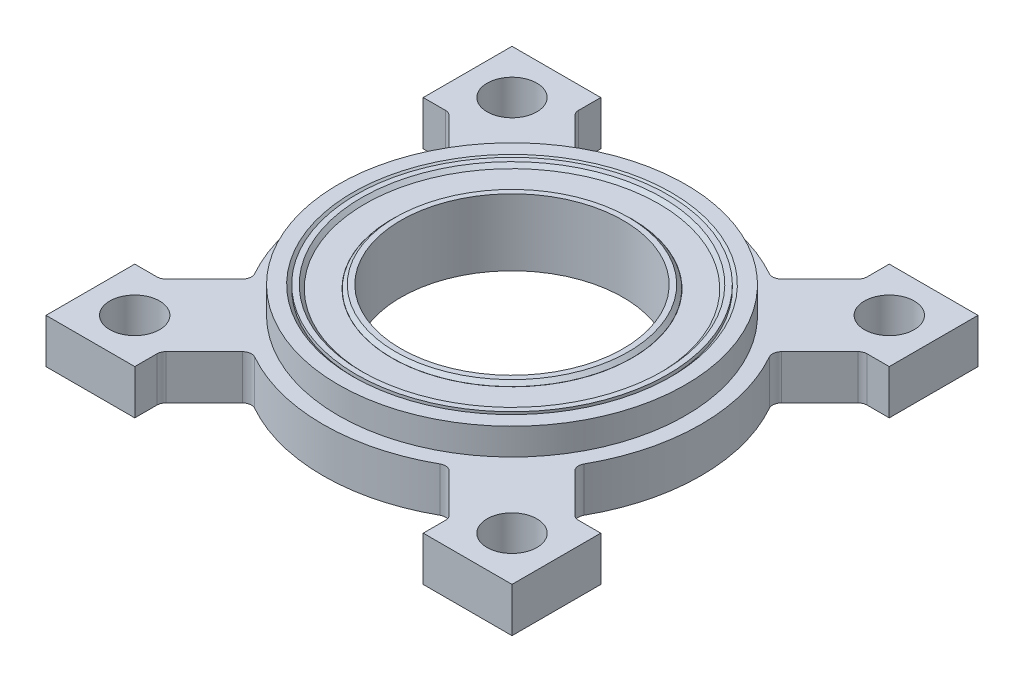
SolidWorks part; units mm, degrees
material "6061 Alloy"
ref_plane "Front Plane" through (0, 0, 0) normal (0, 0, 1) x (1, 0, 0)
ref_plane "Top Plane" through (0, 0, 0) normal (0, 1, 0) x (1, 0, 0)
ref_plane "Right Plane" through (0, 0, 0) normal (1, 0, 0) x (0, 0, -1)
sketch "Sketch1" plane through (0, 0, 0) normal (0, 1, 0) x (1, 0, 0)
  line L0 (-10.2997, 16.637) -> (-10.2997, 15.0529)
  line L1 (-16.637, -16.637) -> (-10.2997, -16.637)
  line L2 (-16.637, -16.637) -> (-16.637, -10.2997)
  line L3 (-16.637, 16.637) -> (-10.2997, 16.637)
  line L4 (16.637, -16.637) -> (16.637, -10.2997)
  line L5 (10.2997, 16.637) -> (16.637, 16.637)
  line L6 (-10.1137, 14.6038) -> (-7.0286, 11.5187)
  line L7 (-16.637, 10.2997) -> (-15.0529, 10.2997)
  line L8 (-16.637, -10.2997) -> (-15.0529, -10.2997)
  line L9 (10.2997, 16.637) -> (10.2997, 15.0529)
  line L10 (-10.2997, -15.0529) -> (-10.2997, -16.637)
  line L11 (-10.1137, -14.6038) -> (-7.3754, -11.8655)
  line L12 (15.0529, 10.2997) -> (16.637, 10.2997)
  line L13 (-14.6038, -10.1137) -> (-11.8655, -7.3754)
  line L14 (10.2997, -15.0529) -> (10.2997, -16.637)
  line L15 (-14.6038, 10.1137) -> (-11.8655, 7.3754)
  line L16 (15.0529, -10.2997) -> (16.637, -10.2997)
  line L17 (14.6038, 10.1137) -> (11.8655, 7.3754)
  line L18 (10.1137, 14.6038) -> (7.3754, 11.8655)
  line L19 (10.1137, -14.6038) -> (7.3754, -11.8655)
  line L20 (14.6038, -10.1137) -> (11.8655, -7.3754)
  line L21 (0, 0) -> (-16.637, -16.637) construction
  line L22 (-16.637, 10.2997) -> (-16.637, 16.637)
  line L23 (10.2997, -16.637) -> (16.637, -16.637)
  line L24 (16.637, 10.2997) -> (16.637, 16.637)
  circle A0 centre (0, 0) radius 11.1252
  circle A1 centre (-13.4704, -13.4704) radius 1.778
  circle A2 centre (-13.4704, 13.4704) radius 1.778
  circle A3 centre (13.4704, 13.4704) radius 1.778
  circle A4 centre (13.4704, -13.4704) radius 1.778
  arc A5 (11.761, -6.6151) -> (11.761, 6.6151) centre (0, 0) ccw
  arc A6 (-6.6151, -11.761) -> (6.6151, -11.761) centre (0, 0) ccw
  arc A7 (-11.761, 6.6151) -> (-11.761, -6.6151) centre (0, 0) ccw
  arc A8 (6.6151, 11.761) -> (-7.0286, 11.5187) centre (0, 0) ccw
  arc A9 (7.3754, 11.8655) -> (6.6151, 11.761) centre (6.9264, 12.3145) cw
  arc A10 (10.1137, 14.6038) -> (10.2997, 15.0529) centre (9.6647, 15.0529) ccw
  arc A11 (14.6038, 10.1137) -> (15.0529, 10.2997) centre (15.0529, 9.6647) cw
  arc A12 (11.8655, 7.3754) -> (11.761, 6.6151) centre (12.3145, 6.9264) ccw
  arc A13 (14.6038, -10.1137) -> (15.0529, -10.2997) centre (15.0529, -9.6647) ccw
  arc A14 (11.8655, -7.3754) -> (11.761, -6.6151) centre (12.3145, -6.9264) cw
  arc A15 (7.3754, -11.8655) -> (6.6151, -11.761) centre (6.9264, -12.3145) ccw
  arc A16 (10.1137, -14.6038) -> (10.2997, -15.0529) centre (9.6647, -15.0529) cw
  arc A17 (-10.1137, -14.6038) -> (-10.2997, -15.0529) centre (-9.6647, -15.0529) ccw
  arc A18 (-7.3754, -11.8655) -> (-6.6151, -11.761) centre (-6.9264, -12.3145) cw
  arc A19 (-14.6038, -10.1137) -> (-15.0529, -10.2997) centre (-15.0529, -9.6647) cw
  arc A20 (-11.8655, -7.3754) -> (-11.761, -6.6151) centre (-12.3145, -6.9264) ccw
  arc A21 (-11.8655, 7.3754) -> (-11.761, 6.6151) centre (-12.3145, 6.9264) cw
  arc A22 (-10.1137, 14.6038) -> (-10.2997, 15.0529) centre (-9.6647, 15.0529) cw
  arc A23 (-14.6038, 10.1137) -> (-15.0529, 10.2997) centre (-15.0529, 9.6647) ccw
  circle A24 centre (0, 0) radius 12.3952 construction
  dimension "D1" = 33.274
  dimension "D3" = 22.2504
  dimension "D4" = 16.637
  dimension "D5" = 3.556
  dimension "D11" = 4
  dimension "D13" = 26.9875
  dimension "D12" = 0.635
  dimension "D15" = 24.7904
  dimension "D2" = 33.274
  dimension "D7" = 10.2997
  dimension "D8" = 20.5994
  dimension "D9" = 20.5994
  dimension "D10" = 10.2997
  dimension "D14" = 16.637
  dimension "D6" = 19.05
extrude "Boss-Extrude1" add sketch "Sketch1" along normal blind 3.175
sketch "Sketch2" plane through (0, 3.175, 0) normal (0, 1, 0) x (1, 0, 0)
  circle A0 centre (0, 0) radius 11.1252
  circle A1 centre (0, 0) radius 12.3952
  dimension "D1" = 24.7904
  dimension "D2" = 22.2504
extrude "Boss-Extrude2" add sketch "Sketch2" along normal blind 1.905
chamfer "Chamfer1" distance 0.254 angle 45 1 edges at (0, 5.08, 11.1252)
sketch "Sketch3" plane through (0, 5.08, 0) normal (0, 1, 0) x (1, 0, 0)
  circle A0 centre (0, 0) radius 11.1252
  circle A1 centre (0, 0) radius 10.4902
  dimension "D2" = 22.2504
  dimension "D1" = 0.635
extrude "Boss-Extrude3" add sketch "Sketch3" against normal blind 4.7625
chamfer "Chamfer2" distance 0.254 angle 45 2 edges at (0, 5.08, 10.4902) (0, 0.3175, 10.4902)
ref_plane "Plane1" through (0, 4.826, 0) normal (0, -1, 0) x (1, 0, 0)
sketch "Sketch4" plane through (0, 4.826, 0) normal (0, -1, 0) x (1, 0, 0)
  circle A0 centre (0, 0) radius 10.4902
  circle A1 centre (0, 0) radius 7.9502 construction
  circle A2 centre (0, 0) radius 8.5852
  dimension "D3" = 20.9804
  dimension "D1" = 2.54
  dimension "D2" = 0.635
extrude "Boss-Extrude4" add sketch "Sketch4" along normal blind 4.2545
sketch "Sketch5" plane through (0, 5.08, 0) normal (0, 1, 0) x (1, 0, 0)
  circle A0 centre (0, 0) radius 8.5725
  circle A1 centre (0, 0) radius 7.9375
  dimension "D1" = 17.145
  dimension "D2" = 15.875
extrude "Boss-Extrude5" add sketch "Sketch5" against normal blind 4.7625
chamfer "Chamfer3" distance 0.254 angle 45 2 edges at (0, 0.3175, 8.5725) (0, 5.08, 8.5725)
